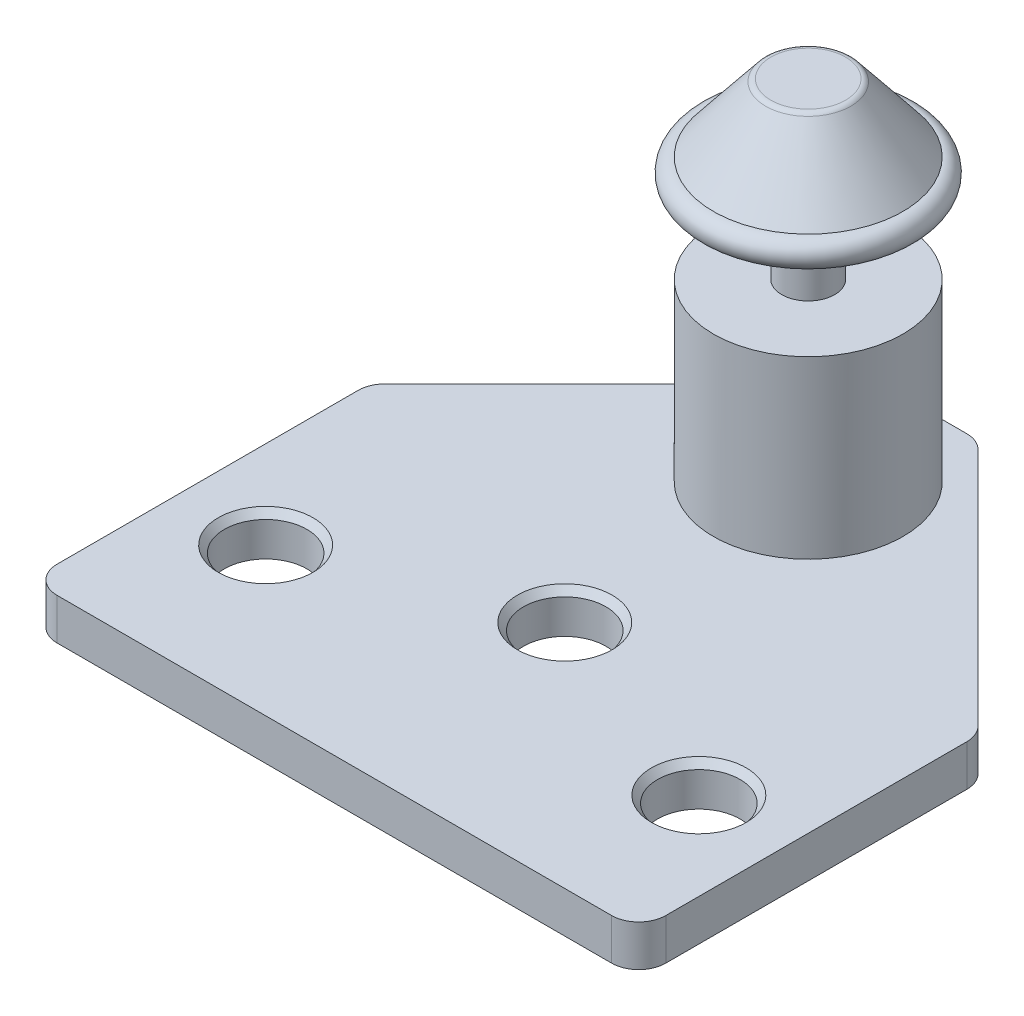
SolidWorks part; units mm, degrees
ref_plane "Front" through (0, 0, 0) normal (0, 0, 1) x (1, 0, 0)
ref_plane "Top" through (0, 0, 0) normal (0, 1, 0) x (1, 0, 0)
ref_plane "Right" through (0, 0, 0) normal (1, 0, 0) x (0, 0, -1)
sketch "Sketch1" plane through (0, 0, 0) normal (0, 1, 0) x (1, 0, 0)
  line L0 (-22.479, -25.063) -> (-22.479, 0)
  line L1 (-22.479, 0) -> (-3.6, 18.879)
  line L2 (-3.6, 18.879) -> (3.6, 18.879)
  line L3 (3.6, 18.879) -> (22.479, 0)
  line L4 (22.479, 0) -> (22.479, -25.063)
  line L5 (22.479, -25.063) -> (-22.479, -25.063)
  line L6 (-22.479, 0) -> (22.479, 0) construction
  dimension "D1" = 44.958
  dimension "D2" = 43.942
  dimension "D3" = 45
  dimension "D4" = 7.2
extrude "Extrude1" add sketch "Sketch1" along normal blind 3.048
hole_wizard "Hole1" positions "Sketch3" profile "Sketch2" legacy end condition through all
sketch "Sketch3" plane through (0, 3.048, 0) normal (0, 1, 0) x (-1, 0, 0)
  line L0 (-16, 14.141) -> (16, 14.141) construction
  line L3 (0, 8.045) -> (0, 14.141) construction
  line L6 (22.479, 25.063) -> (-22.479, 25.063) construction
  point P0 (0, 8.045)
  point P3 (-16, 14.141)
  point P5 (16, 14.141)
  dimension "D1" = 10.922
  dimension "D2" = 6.096
  dimension "D3" = 32
sketch "Sketch2" plane through (0, 3.048, 8.045) normal (1, 0, 0) x (0, 0, 1)
  line L0 (0, 0) -> (0, 3.048)
  line L1 (0, 3.048) -> (3.048, 3.048)
  line L2 (3.048, 3.048) -> (3.048, 0.52)
  line L3 (3.048, 0.52) -> (3.5, 0)
  line L4 (3.5, 0) -> (0, 0)
  line L5 (0, -6.4453) -> (0, 115.525) construction
  line L6 (-3.048, 0.52) -> (-3.5, 0) construction
  dimension "Diameter" = 6.096
  dimension "Depth" = 3.048
  dimension "C-Sink Angle" = 82
  dimension "C-Sink Diameter" = 7
sketch "Sketch4" plane through (0, 3.048, 0) normal (0, 1, 0) x (-1, 0, 0)
  line L3 (22.479, 25.063) -> (-22.479, 25.063) construction
  line L4 (0, 0) -> (0, -9.937) construction
  circle A0 centre (0, -9.937) radius 7
  dimension "D1" = 35
  dimension "D2" = 14
extrude "Extrude2" add sketch "Sketch4" along normal blind 12.954
sketch "Sketch5" plane through (0, 16.002, 0) normal (0, 1, 0) x (-1, 0, 0)
  circle A0 centre (0, -9.937) radius 1.9558
  dimension "D1" = 3.9116
extrude "Extrude3" add sketch "Sketch5" along normal blind 5.842
sketch "Sketch6" plane through (0, 21.844, 0) normal (0, 1, 0) x (-1, 0, 0)
  circle A0 centre (0, -9.937) radius 1.5
  dimension "D1" = 3
extrude "Extrude4" add sketch "Sketch6" along normal blind 1.4
sketch "Sketch7" plane through (0, 23.244, 0) normal (0, 1, 0) x (-1, 0, 0)
  circle A0 centre (0, -9.937) radius 1.9558 construction
  circle A1 centre (0, -9.937) radius 1.9558
extrude "Extrude6" add sketch "Sketch7" along normal blind 3.1
ref_plane "Plane1" through (0, 0, -9.937) normal (0, 0, 1) x (1, 0, 0)
sketch "Sketch8" plane through (0, 0, -9.937) normal (0, 0, 1) x (1, 0, 0)
  line L0 (0, 21.844) -> (7, 21.844) construction
  line L1 (7, 23.844) -> (3, 28.844)
  line L2 (3, 28.844) -> (0, 28.844)
  line L3 (0, 28.844) -> (0, 21.844) construction
  line L4 (0, 21.844) -> (0, 0) construction
  line L5 (1.9558, 21.844) -> (-1.9558, 21.844) construction
  line L6 (0, 28.844) -> (0, 26.494)
  line L7 (0, 26.494) -> (2.0558, 26.494)
  line L8 (2.0558, 26.494) -> (2.0558, 21.844)
  line L9 (2.0558, 21.844) -> (7, 21.844)
  line L10 (1.9558, 23.244) -> (1.9558, 26.344) construction
  line L11 (1.9558, 26.344) -> (-1.9558, 26.344) construction
  line L12 (1.9558, 16.002) -> (1.9558, 21.844) construction
  line L13 (1.9558, 26.344) -> (-1.9558, 26.344) construction
  line L14 (1.9558, 16.002) -> (1.9558, 21.844) construction
  line L15 (7, 16.002) -> (-7, 16.002) construction
  line L16 (-1.9558, 21.844) -> (-1.9558, 16.002) construction
  line L17 (-1.9558, 21.844) -> (-1.9558, 16.002) construction
  arc A0 (7, 21.844) -> (7, 23.844) centre (7, 22.844) ccw
  dimension "D2" = 16
  dimension "D1" = 7
  dimension "D3" = 6
  dimension "D4" = 2
  dimension "D5" = 0.1
  dimension "D6" = 0.15
  dimension "D7" = 10.342
  dimension "D8" = 3.9116
revolve "Revolve1" add sketch "Sketch8" angle 360 about L4
fillet "Fillet1" radius 0.5 1 edges at (-3, 28.844, -9.937)
fillet "Fillet2" radius 2 6 edges at (3.6, 1.524, -18.879) (22.479, 1.524, 0) (22.479, 1.524, 25.063) (-22.479, 1.524, 25.063) (-22.479, 1.524, 0) (-3.6, 1.524, -18.879)
